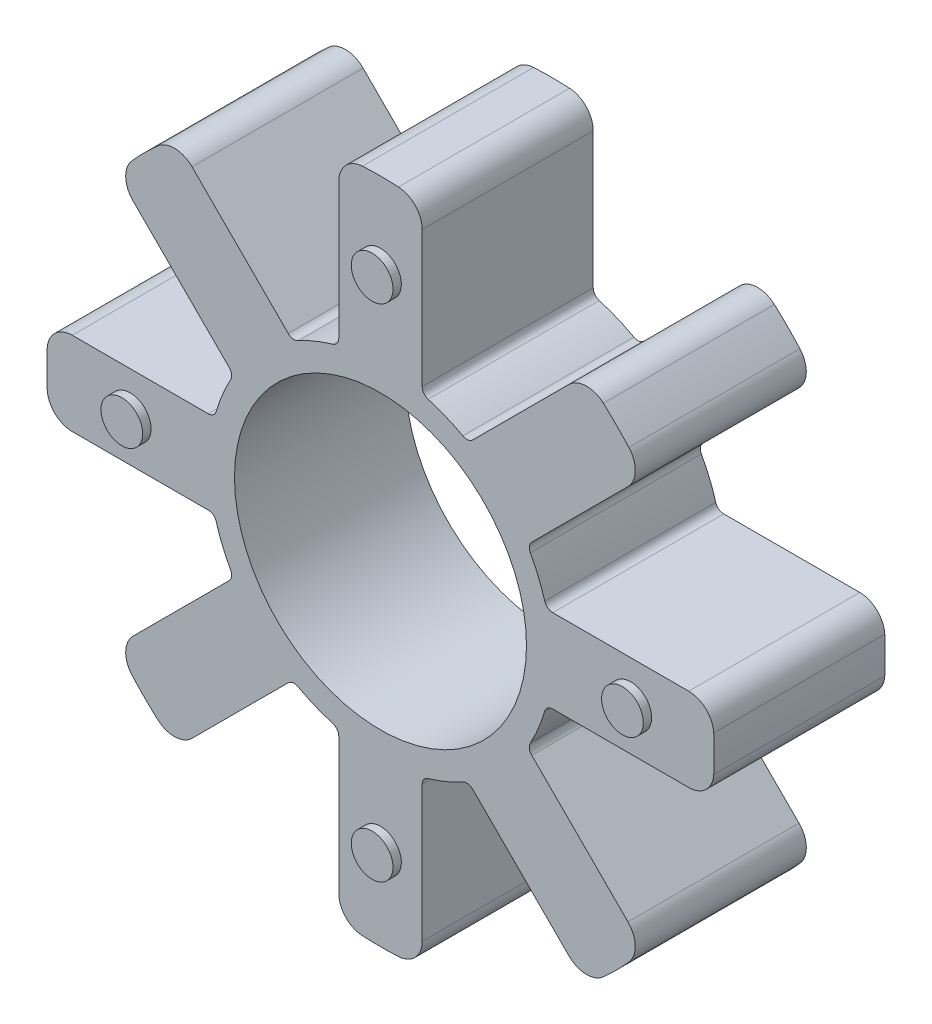
SolidWorks part; units mm, degrees
ref_plane "Front Plane" through (0, 0, 0) normal (0, 0, 1) x (1, 0, 0)
ref_plane "Top Plane" through (0, 0, 0) normal (0, 1, 0) x (1, 0, 0)
ref_plane "Right Plane" through (0, 0, 0) normal (1, 0, 0) x (0, 0, -1)
sketch "Sketch1" plane through (0, 0, 0) normal (0, 0, 1) x (1, 0, 0)
  line L0 (-5, 36.9459) -> (-5, 20.6458)
  line L1 (5, 36.9459) -> (5, 20.6458)
  line L2 (-5, 28.7959) -> (5, 28.7959) construction
  line L3 (22.5892, 29.6602) -> (11.0633, 18.1343)
  line L4 (29.6602, 22.5892) -> (18.1343, 11.0633)
  line L5 (36.9459, 5) -> (20.6458, 5)
  line L6 (36.9459, -5) -> (20.6458, -5)
  line L7 (29.6602, -22.5892) -> (18.1343, -11.0633)
  line L8 (22.5892, -29.6602) -> (11.0633, -18.1343)
  line L9 (5, -36.9459) -> (5, -20.6458)
  line L10 (-5, -36.9459) -> (-5, -20.6458)
  line L11 (-22.5892, -29.6602) -> (-11.0633, -18.1343)
  line L12 (-29.6602, -22.5892) -> (-18.1343, -11.0633)
  line L13 (-36.9459, -5) -> (-20.6458, -5)
  line L14 (-36.9459, 5) -> (-20.6458, 5)
  line L15 (-29.6602, 22.5892) -> (-18.1343, 11.0633)
  line L16 (-22.5892, 29.6602) -> (-11.0633, 18.1343)
  circle A0 centre (0, 0) radius 30 construction
  arc A1 (-5.7209, 19.6856) -> (-9.8745, 17.9651) centre (0, 0) ccw
  circle A2 centre (0, 0) radius 17.5
  arc A3 (2.1622, 39.9415) -> (-2.1622, 39.9415) centre (0, 0) ccw
  arc A4 (5, 36.9459) -> (2.1622, 39.9415) centre (2, 36.9459) ccw
  arc A5 (-5, 36.9459) -> (-2.1622, 39.9415) centre (-2, 36.9459) cw
  arc A6 (5, 20.6458) -> (5.7209, 19.6856) centre (6, 20.6458) ccw
  arc A7 (-5, 20.6458) -> (-5.7209, 19.6856) centre (-6, 20.6458) cw
  arc A8 (11.0633, 18.1343) -> (9.8745, 17.9651) centre (10.3562, 18.8414) cw
  arc A9 (22.5892, 29.6602) -> (26.714, 29.7718) centre (24.7105, 27.5389) cw
  arc A10 (29.7718, 26.714) -> (26.714, 29.7718) centre (0, 0) ccw
  arc A11 (29.6602, 22.5892) -> (29.7718, 26.714) centre (27.5389, 24.7105) ccw
  arc A12 (18.1343, 11.0633) -> (17.9651, 9.8745) centre (18.8414, 10.3562) ccw
  arc A13 (20.6458, 5) -> (19.6856, 5.7209) centre (20.6458, 6) cw
  arc A14 (36.9459, 5) -> (39.9415, 2.1622) centre (36.9459, 2) cw
  arc A15 (39.9415, -2.1622) -> (39.9415, 2.1622) centre (0, 0) ccw
  arc A16 (36.9459, -5) -> (39.9415, -2.1622) centre (36.9459, -2) ccw
  arc A17 (20.6458, -5) -> (19.6856, -5.7209) centre (20.6458, -6) ccw
  arc A18 (18.1343, -11.0633) -> (17.9651, -9.8745) centre (18.8414, -10.3562) cw
  arc A19 (29.6602, -22.5892) -> (29.7718, -26.714) centre (27.5389, -24.7105) cw
  arc A20 (26.714, -29.7718) -> (29.7718, -26.714) centre (0, 0) ccw
  arc A21 (22.5892, -29.6602) -> (26.714, -29.7718) centre (24.7105, -27.5389) ccw
  arc A22 (11.0633, -18.1343) -> (9.8745, -17.9651) centre (10.3562, -18.8414) ccw
  arc A23 (5, -20.6458) -> (5.7209, -19.6856) centre (6, -20.6458) cw
  arc A24 (5, -36.9459) -> (2.1622, -39.9415) centre (2, -36.9459) cw
  arc A25 (-2.1622, -39.9415) -> (2.1622, -39.9415) centre (0, 0) ccw
  arc A26 (-5, -36.9459) -> (-2.1622, -39.9415) centre (-2, -36.9459) ccw
  arc A27 (-5, -20.6458) -> (-5.7209, -19.6856) centre (-6, -20.6458) ccw
  arc A28 (-11.0633, -18.1343) -> (-9.8745, -17.9651) centre (-10.3562, -18.8414) cw
  arc A29 (-22.5892, -29.6602) -> (-26.714, -29.7718) centre (-24.7105, -27.5389) cw
  arc A30 (-29.7718, -26.714) -> (-26.714, -29.7718) centre (0, 0) ccw
  arc A31 (-29.6602, -22.5892) -> (-29.7718, -26.714) centre (-27.5389, -24.7105) ccw
  arc A32 (-18.1343, -11.0633) -> (-17.9651, -9.8745) centre (-18.8414, -10.3562) ccw
  arc A33 (-20.6458, -5) -> (-19.6856, -5.7209) centre (-20.6458, -6) cw
  arc A34 (-36.9459, -5) -> (-39.9415, -2.1622) centre (-36.9459, -2) cw
  arc A35 (-39.9415, 2.1622) -> (-39.9415, -2.1622) centre (0, 0) ccw
  arc A36 (-36.9459, 5) -> (-39.9415, 2.1622) centre (-36.9459, 2) ccw
  arc A37 (-20.6458, 5) -> (-19.6856, 5.7209) centre (-20.6458, 6) ccw
  arc A38 (-18.1343, 11.0633) -> (-17.9651, 9.8745) centre (-18.8414, 10.3562) cw
  arc A39 (-29.6602, 22.5892) -> (-29.7718, 26.714) centre (-27.5389, 24.7105) cw
  arc A40 (-26.714, 29.7718) -> (-29.7718, 26.714) centre (0, 0) ccw
  arc A41 (-22.5892, 29.6602) -> (-26.714, 29.7718) centre (-24.7105, 27.5389) ccw
  arc A42 (-11.0633, 18.1343) -> (-9.8745, 17.9651) centre (-10.3562, 18.8414) ccw
  arc A43 (-17.9651, 9.8745) -> (-19.6856, 5.7209) centre (0, 0) ccw
  arc A44 (9.8745, 17.9651) -> (5.7209, 19.6856) centre (0, 0) ccw
  arc A45 (19.6856, 5.7209) -> (17.9651, 9.8745) centre (0, 0) ccw
  arc A46 (17.9651, -9.8745) -> (19.6856, -5.7209) centre (0, 0) ccw
  arc A47 (5.7209, -19.6856) -> (9.8745, -17.9651) centre (0, 0) ccw
  arc A48 (-9.8745, -17.9651) -> (-5.7209, -19.6856) centre (0, 0) ccw
  arc A49 (-19.6856, -5.7209) -> (-17.9651, -9.8745) centre (0, 0) ccw
  point P12 (0, 28.7959)
  point P105 (0, 0)
  dimension "D1" = 60
  dimension "D2" = 41
  dimension "D3" = 35
  dimension "D4" = 80
  dimension "D6" = 3
  dimension "D7" = 1
  dimension "D5" = 10
  dimension "D8" = 8
extrude "Boss-Extrude1" add sketch "Sketch1" along normal mid plane 20.5
sketch "Sketch2" plane through (0, 0, 10.25) normal (0, 0, 1) x (1, 0, 0)
  circle A0 centre (0, 30) radius 2.5
  circle A1 centre (0, 0) radius 30 construction
  circle A2 centre (30, 0) radius 2.5
  circle A3 centre (0, -30) radius 2.5
  circle A4 centre (-30, 0) radius 2.5
  point P2 (-30, 0)
  point P5 (0, 0)
  point P14 (0, 0)
  dimension "D1" = 5
  dimension "D2" = 4
extrude "Boss-Extrude2" add sketch "Sketch2" along normal blind 1
mirror "Mirror1" about plane through (0, 0, 0) normal (0, 0, 1) of "Boss-Extrude2"
